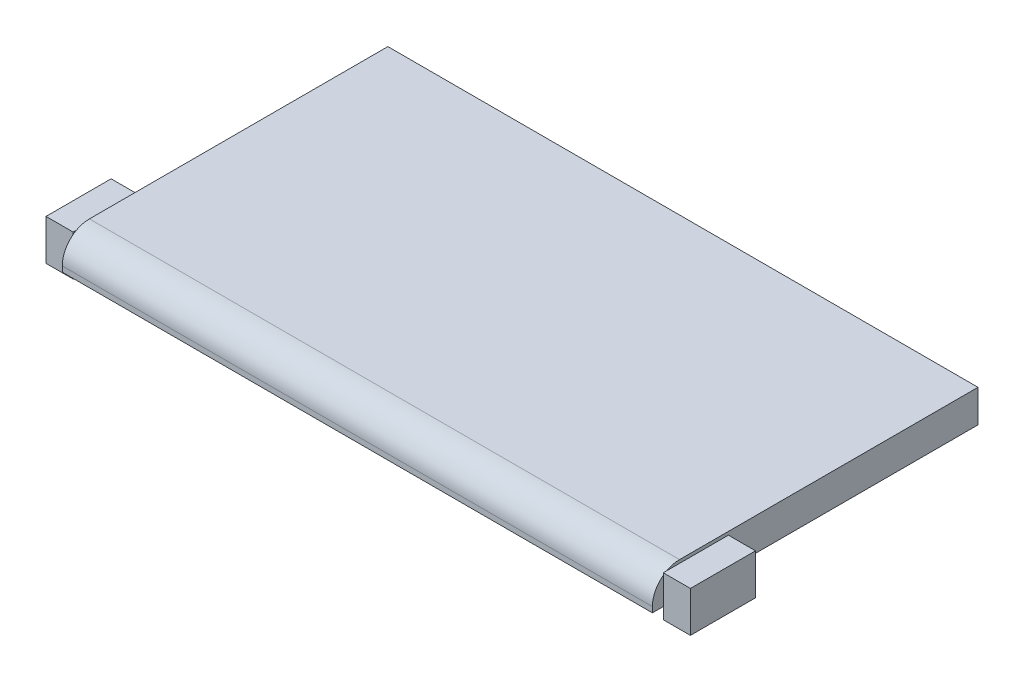
SolidWorks part; units mm, degrees
material "AISI 4130 Steel, normalized at 870C"
ref_plane "Front Plane" through (0, 0, 0) normal (0, 0, 1) x (1, 0, 0)
ref_plane "Top Plane" through (0, 0, 0) normal (0, 1, 0) x (1, 0, 0)
ref_plane "Right Plane" through (0, 0, 0) normal (1, 0, 0) x (0, 0, -1)
sketch "Sketch1" plane through (0, 0, 0) normal (0, 1, 0) x (1, 0, 0)
  line L0 (0, 149.352) -> (0, 150.876) construction
  line L1 (0, 0) -> (273.177, 0)
  line L2 (0, 0) -> (0, 149.352)
  line L3 (0, 149.352) -> (273.177, 149.352)
  line L4 (273.177, 0) -> (273.177, 149.352)
  line L5 (-1.524, -1.524) -> (274.701, -1.524)
  line L6 (-1.524, -1.524) -> (-1.524, 150.876)
  line L7 (-1.524, 150.876) -> (274.701, 150.876)
  line L8 (274.701, -1.524) -> (274.701, 150.876)
  line L9 (273.177, 149.352) -> (274.701, 149.352) construction
  line L10 (273.177, 0) -> (273.177, -1.524) construction
  line L11 (0, 0) -> (-1.524, 0) construction
  line L13 (0, 0) -> (273.177, 0)
  line L14 (0, 0) -> (0, 149.352)
  line L15 (0, 149.352) -> (273.177, 149.352)
  line L16 (273.177, 0) -> (273.177, 149.352)
  dimension "D1" = 1.524
  dimension "D2" = 276.225
  dimension "D3" = 152.4
extrude "Bulk-Extrude" add sketch "Sketch1" along normal blind 15.24 contours L1 L4 L3 L2 | L5 L8 L7 L6 L4 L1 L2 L3
fillet "Fillet1" radius 12.7 1 edges at (136.5885, 15.24, 1.524)
shell "Shell" thickness 1.524
ref_plane "Mid Plane" through (136.5885, 0, 0) normal (1, 0, 0) x (0, 0, -1)
sketch "Sketch2" plane through (136.5885, 0, 0) normal (1, 0, 0) x (0, 0, -1)
  line L0 (150.876, 0) -> (154.051, 0)
  line L1 (154.051, 3.175) -> (150.876, 3.175)
  line L2 (150.876, 15.24) -> (150.876, 0) construction
  line L3 (150.876, 3.175) -> (150.876, 0)
  circle A0 centre (154.051, 0) radius 3.175
  circle A1 centre (154.051, 0) radius 1.651
  dimension "D1" = 1.524
  dimension "D2" = 6.35
extrude "Boss-Extrude3" add sketch "Sketch2" along normal mid plane 101.6
sketch "Sketch3" plane through (274.701, 0, 0) normal (1, 0, 0) x (0, 0, -1)
  line L0 (-1.524, 2.54) -> (-1.524, 0) construction
  line L1 (3.556, 13.716) -> (34.036, 13.716)
  line L2 (3.556, 13.716) -> (3.556, -5.334)
  line L3 (3.556, -5.334) -> (34.036, -5.334)
  line L4 (34.036, 13.716) -> (34.036, -5.334)
  line L5 (11.176, 15.24) -> (150.876, 15.24) construction
  dimension "D1" = 5.08
  dimension "D2" = 1.524
  dimension "D3" = 30.48
  dimension "D4" = 19.05
extrude "Latch Clear. Hook, Right-Extrude" add sketch "Sketch3" along normal blind 12.7 separate body
mirror "Latch Clear. Hook, Left-Mirror" about plane through (136.5885, 0, 0) normal (1, 0, 0) of "Latch Clear. Hook, Right-Extrude"
